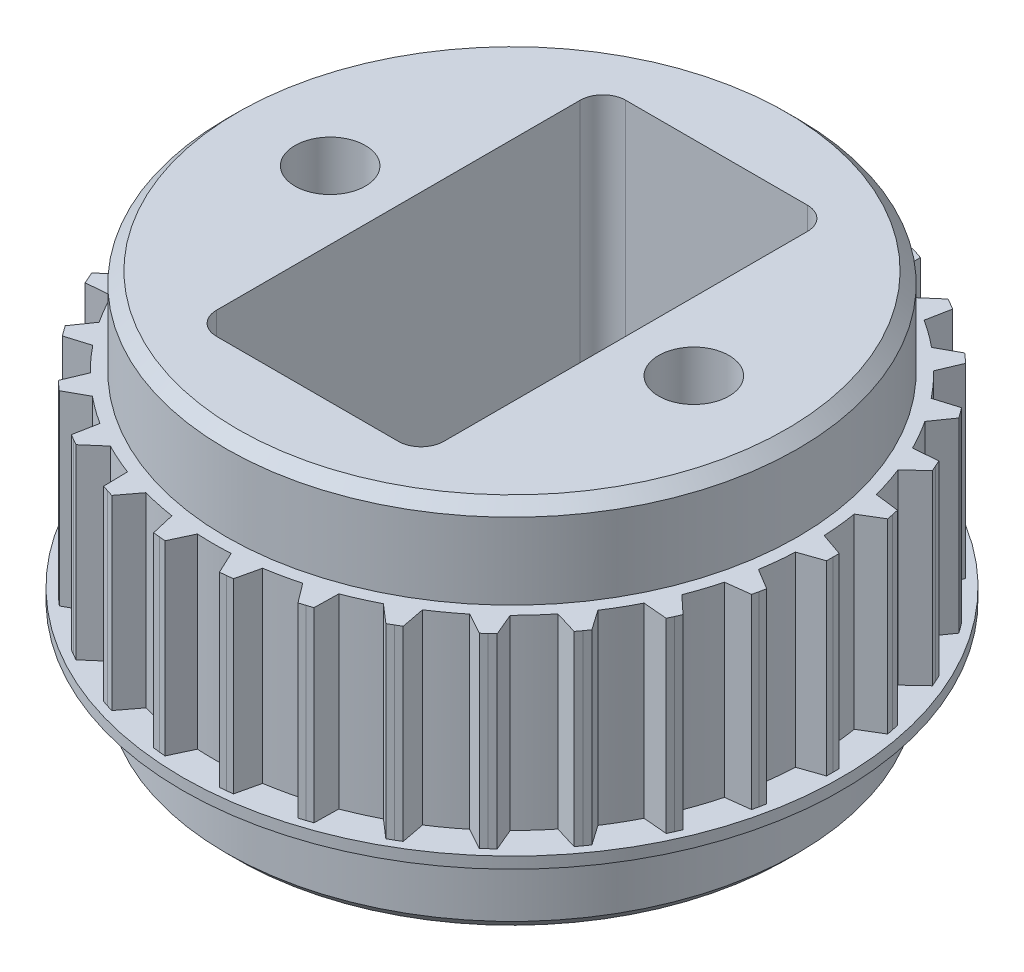
SolidWorks part; units mm, degrees
ref_plane "Front Plane" through (0, 0, 0) normal (0, 0, 1) x (1, 0, 0)
ref_plane "Top Plane" through (0, 0, 0) normal (0, 1, 0) x (1, 0, 0)
ref_plane "Right Plane" through (0, 0, 0) normal (1, 0, 0) x (0, 0, -1)
sketch "Sketch1" plane through (0, 0, 0) normal (0, 1, 0) x (1, 0, 0)
  line L0 (0, 0) -> (-13.12, 0) construction
  line L1 (-13.12, 0) -> (-15.3941, 0) construction
  line L4 (-14.12, 0) -> (-14.1172, 0.28)
  line L5 (-14.1172, 0.28) -> (-13.1049, 0.63)
  line L6 (-14.12, 0) -> (-14.1172, -0.28)
  line L7 (-14.1172, -0.28) -> (-13.1049, -0.63)
  line L8 (-13.7505, 3.209) -> (-12.6875, 3.3409)
  line L9 (-13.8669, 2.6613) -> (-12.9495, 2.1084)
  line L10 (-13.8114, 2.9357) -> (-13.8669, 2.6613)
  line L11 (-13.8114, 2.9357) -> (-13.7505, 3.209)
  line L12 (-12.7828, 5.9978) -> (-11.7156, 5.9058)
  line L13 (-13.0106, 5.4862) -> (-12.2281, 4.7547)
  line L14 (-12.8993, 5.7431) -> (-13.0106, 5.4862)
  line L15 (-12.8993, 5.7431) -> (-12.7828, 5.9978)
  line L16 (-11.2565, 8.5244) -> (-10.2318, 8.2125)
  line L17 (-11.5857, 8.0714) -> (-10.9724, 7.1932)
  line L18 (-11.4233, 8.2995) -> (-11.5857, 8.0714)
  line L19 (-11.4233, 8.2995) -> (-11.2565, 8.5244)
  line L20 (-9.2382, 10.6785) -> (-8.3007, 10.1604)
  line L21 (-9.6543, 10.3038) -> (-9.237, 9.3173)
  line L22 (-9.4481, 10.4932) -> (-9.6543, 10.3038)
  line L23 (-9.4481, 10.4932) -> (-9.2382, 10.6785)
  line L24 (-6.8161, 12.3659) -> (-6.0068, 11.6641)
  line L25 (-7.3011, 12.0859) -> (-7.098, 11.0341)
  line L26 (-7.06, 12.2283) -> (-7.3011, 12.0859)
  line L27 (-7.06, 12.2283) -> (-6.8161, 12.3659)
  line L28 (-4.0962, 13.5128) -> (-3.4505, 12.6581)
  line L29 (-4.6288, 13.3398) -> (-4.6488, 12.2688)
  line L30 (-4.3633, 13.4289) -> (-4.6288, 13.3398)
  line L31 (-4.3633, 13.4289) -> (-4.0962, 13.5128)
  line L32 (-1.1972, 14.0692) -> (-0.7433, 13.0989)
  line L33 (-1.7541, 14.0106) -> (-1.9964, 12.9672)
  line L34 (-1.4759, 14.0426) -> (-1.7541, 14.0106)
  line L35 (-1.4759, 14.0426) -> (-1.1972, 14.0692)
  line L36 (1.7541, 14.0106) -> (1.9964, 12.9672)
  line L37 (1.1972, 14.0692) -> (0.7433, 13.0989)
  line L38 (1.4759, 14.0426) -> (1.1972, 14.0692)
  line L39 (1.4759, 14.0426) -> (1.7541, 14.0106)
  line L40 (4.6287, 13.3398) -> (4.6488, 12.2688)
  line L41 (4.0962, 13.5128) -> (3.4505, 12.6581)
  line L42 (4.3633, 13.4289) -> (4.0962, 13.5128)
  line L43 (4.3633, 13.4289) -> (4.6287, 13.3398)
  line L44 (7.3011, 12.0859) -> (7.098, 11.0341)
  line L45 (6.8161, 12.3659) -> (6.0068, 11.6641)
  line L46 (7.06, 12.2283) -> (6.8161, 12.3659)
  line L47 (7.06, 12.2283) -> (7.3011, 12.0859)
  line L48 (9.6543, 10.3038) -> (9.237, 9.3173)
  line L49 (9.2382, 10.6785) -> (8.3007, 10.1604)
  line L50 (9.4481, 10.4932) -> (9.2382, 10.6785)
  line L51 (9.4481, 10.4932) -> (9.6543, 10.3038)
  line L52 (11.5856, 8.0714) -> (10.9724, 7.1932)
  line L53 (11.2565, 8.5244) -> (10.2318, 8.2125)
  line L54 (11.4233, 8.2995) -> (11.2565, 8.5244)
  line L55 (11.4233, 8.2995) -> (11.5856, 8.0714)
  line L56 (13.0106, 5.4862) -> (12.2281, 4.7547)
  line L57 (12.7828, 5.9978) -> (11.7156, 5.9058)
  line L58 (12.8993, 5.7431) -> (12.7828, 5.9978)
  line L59 (12.8993, 5.7431) -> (13.0106, 5.4862)
  line L60 (13.8669, 2.6613) -> (12.9495, 2.1084)
  line L61 (13.7505, 3.209) -> (12.6875, 3.3409)
  line L62 (13.8114, 2.9357) -> (13.7505, 3.209)
  line L63 (13.8114, 2.9357) -> (13.8669, 2.6613)
  line L64 (14.1172, -0.28) -> (13.1049, -0.63)
  line L65 (14.1172, 0.28) -> (13.1049, 0.63)
  line L66 (14.12, 0) -> (14.1172, 0.28)
  line L67 (14.12, 0) -> (14.1172, -0.28)
  line L68 (13.7505, -3.209) -> (12.6875, -3.3409)
  line L69 (13.8669, -2.6613) -> (12.9495, -2.1084)
  line L70 (13.8114, -2.9357) -> (13.8669, -2.6613)
  line L71 (13.8114, -2.9357) -> (13.7505, -3.209)
  line L72 (12.7828, -5.9978) -> (11.7156, -5.9058)
  line L73 (13.0106, -5.4862) -> (12.2281, -4.7547)
  line L74 (12.8993, -5.7431) -> (13.0106, -5.4862)
  line L75 (12.8993, -5.7431) -> (12.7828, -5.9978)
  line L76 (11.2565, -8.5244) -> (10.2318, -8.2125)
  line L77 (11.5857, -8.0714) -> (10.9724, -7.1932)
  line L78 (11.4233, -8.2995) -> (11.5857, -8.0714)
  line L79 (11.4233, -8.2995) -> (11.2565, -8.5244)
  line L80 (9.2382, -10.6785) -> (8.3007, -10.1604)
  line L81 (9.6543, -10.3038) -> (9.237, -9.3173)
  line L82 (9.4481, -10.4932) -> (9.6543, -10.3038)
  line L83 (9.4481, -10.4932) -> (9.2382, -10.6785)
  line L84 (6.8161, -12.3659) -> (6.0068, -11.6641)
  line L85 (7.3011, -12.0859) -> (7.098, -11.0341)
  line L86 (7.06, -12.2283) -> (7.3011, -12.0859)
  line L87 (7.06, -12.2283) -> (6.8161, -12.3659)
  line L88 (4.0962, -13.5128) -> (3.4505, -12.6581)
  line L89 (4.6288, -13.3398) -> (4.6488, -12.2688)
  line L90 (4.3633, -13.4289) -> (4.6288, -13.3398)
  line L91 (4.3633, -13.4289) -> (4.0962, -13.5128)
  line L92 (1.1972, -14.0692) -> (0.7433, -13.0989)
  line L93 (1.7541, -14.0106) -> (1.9964, -12.9672)
  line L94 (1.4759, -14.0426) -> (1.7541, -14.0106)
  line L95 (1.4759, -14.0426) -> (1.1972, -14.0692)
  line L96 (-1.7541, -14.0106) -> (-1.9964, -12.9672)
  line L97 (-1.1972, -14.0692) -> (-0.7433, -13.0989)
  line L98 (-1.4759, -14.0426) -> (-1.1972, -14.0692)
  line L99 (-1.4759, -14.0426) -> (-1.7541, -14.0106)
  line L100 (-4.6287, -13.3398) -> (-4.6488, -12.2688)
  line L101 (-4.0962, -13.5128) -> (-3.4505, -12.6581)
  line L102 (-4.3633, -13.4289) -> (-4.0962, -13.5128)
  line L103 (-4.3633, -13.4289) -> (-4.6287, -13.3398)
  line L104 (-7.3011, -12.0859) -> (-7.098, -11.0341)
  line L105 (-6.8161, -12.3659) -> (-6.0068, -11.6641)
  line L106 (-7.06, -12.2283) -> (-6.8161, -12.3659)
  line L107 (-7.06, -12.2283) -> (-7.3011, -12.0859)
  line L108 (-9.6543, -10.3038) -> (-9.237, -9.3173)
  line L109 (-9.2382, -10.6785) -> (-8.3007, -10.1604)
  line L110 (-9.4481, -10.4932) -> (-9.2382, -10.6785)
  line L111 (-9.4481, -10.4932) -> (-9.6543, -10.3038)
  line L112 (-11.5856, -8.0714) -> (-10.9724, -7.1932)
  line L113 (-11.2565, -8.5244) -> (-10.2318, -8.2125)
  line L114 (-11.4233, -8.2995) -> (-11.2565, -8.5244)
  line L115 (-11.4233, -8.2995) -> (-11.5856, -8.0714)
  line L116 (-13.0106, -5.4862) -> (-12.2281, -4.7547)
  line L117 (-12.7828, -5.9978) -> (-11.7156, -5.9058)
  line L118 (-12.8993, -5.7431) -> (-12.7828, -5.9978)
  line L119 (-12.8993, -5.7431) -> (-13.0106, -5.4862)
  line L120 (-13.8669, -2.6613) -> (-12.9495, -2.1084)
  line L121 (-13.7505, -3.209) -> (-12.6875, -3.3409)
  line L122 (-13.8114, -2.9357) -> (-13.7505, -3.209)
  line L123 (-13.8114, -2.9357) -> (-13.8669, -2.6613)
  circle A0 centre (0, 0) radius 13.12
  circle A2 centre (0, 0) radius 13.12
  circle A3 centre (0, 0) radius 13.12
  circle A4 centre (0, 0) radius 13.12
  circle A5 centre (0, 0) radius 13.12
  circle A6 centre (0, 0) radius 13.12
  circle A7 centre (0, 0) radius 13.12
  circle A8 centre (0, 0) radius 13.12
  circle A9 centre (0, 0) radius 13.12
  circle A10 centre (0, 0) radius 13.12
  circle A11 centre (0, 0) radius 13.12
  circle A12 centre (0, 0) radius 13.12
  circle A13 centre (0, 0) radius 13.12
  circle A14 centre (0, 0) radius 13.12
  circle A15 centre (0, 0) radius 13.12
  circle A16 centre (0, 0) radius 13.12
  circle A17 centre (0, 0) radius 13.12
  circle A18 centre (0, 0) radius 13.12
  circle A19 centre (0, 0) radius 13.12
  circle A20 centre (0, 0) radius 13.12
  circle A21 centre (0, 0) radius 13.12
  circle A22 centre (0, 0) radius 13.12
  circle A23 centre (0, 0) radius 13.12
  circle A24 centre (0, 0) radius 13.12
  circle A25 centre (0, 0) radius 13.12
  circle A26 centre (0, 0) radius 13.12
  circle A27 centre (0, 0) radius 13.12
  circle A28 centre (0, 0) radius 13.12
  circle A29 centre (0, 0) radius 13.12
  circle A30 centre (0, 0) radius 13.12
  point P187 (0, 0)
  dimension "D1" = 26.24
  dimension "D3" = 0.63
  dimension "D4" = 0.63
  dimension "D5" = 0.28
  dimension "D6" = 0.28
  dimension "D2" = 30
sketch "Sketch3" plane through (0, 0, 0) normal (0, 1, 0) x (1, 0, 0)
  circle A0 centre (0, 0) radius 13.12
extrude "Boss-Extrude1" add sketch "Sketch3" along normal blind 8.2
sketch "Sketch4" plane through (0, 0, 0) normal (0, 1, 0) x (1, 0, 0)
  line L0 (-14.1172, -0.28) -> (-13.1049, -0.63) construction
  line L1 (-14.12, 0) -> (-14.1172, -0.28) construction
  line L2 (-14.12, 0) -> (-14.1172, 0.28) construction
  line L3 (-14.1172, 0.28) -> (-13.1049, 0.63) construction
  line L4 (-14.1172, -0.28) -> (-12.8499, -0.7181)
  line L5 (-14.12, 0) -> (-14.1172, -0.28)
  line L6 (-14.12, 0) -> (-14.1172, 0.28)
  line L7 (-14.1172, 0.28) -> (-12.8499, 0.7181)
  line L8 (-13.8669, 2.6613) -> (-12.7185, 1.9692)
  line L9 (-13.8114, 2.9357) -> (-13.8669, 2.6613)
  line L10 (-13.8114, 2.9357) -> (-13.7505, 3.209)
  line L11 (-13.7505, 3.209) -> (-12.4198, 3.3741)
  line L12 (-13.0106, 5.4862) -> (-12.0311, 4.5705)
  line L13 (-12.8993, 5.7431) -> (-13.0106, 5.4862)
  line L14 (-12.8993, 5.7431) -> (-12.7828, 5.9978)
  line L15 (-12.7828, 5.9978) -> (-11.4469, 5.8826)
  line L16 (-11.5857, 8.0714) -> (-10.8179, 6.972)
  line L17 (-11.4233, 8.2995) -> (-11.5857, 8.0714)
  line L18 (-11.4233, 8.2995) -> (-11.2565, 8.5244)
  line L19 (-11.2565, 8.5244) -> (-9.9737, 8.134)
  line L20 (-9.6543, 10.3038) -> (-9.132, 9.0688)
  line L21 (-9.4481, 10.4932) -> (-9.6543, 10.3038)
  line L22 (-9.4481, 10.4932) -> (-9.2382, 10.6785)
  line L23 (-9.2382, 10.6785) -> (-8.0646, 10.0299)
  line L24 (-7.3011, 12.0859) -> (-7.0469, 10.7693)
  line L25 (-7.06, 12.2283) -> (-7.3011, 12.0859)
  line L26 (-7.06, 12.2283) -> (-6.8161, 12.3659)
  line L27 (-6.8161, 12.3659) -> (-5.8031, 11.4874)
  line L28 (-4.6288, 13.3398) -> (-4.6538, 11.9991)
  line L29 (-4.3633, 13.4289) -> (-4.6288, 13.3398)
  line L30 (-4.3633, 13.4289) -> (-4.0962, 13.5128)
  line L31 (-4.0962, 13.5128) -> (-3.2879, 12.4429)
  line L32 (-1.7541, 14.0106) -> (-2.0574, 12.7045)
  line L33 (-1.4759, 14.0426) -> (-1.7541, 14.0106)
  line L34 (-1.4759, 14.0426) -> (-1.1972, 14.0692)
  line L35 (-1.1972, 14.0692) -> (-0.629, 12.8546)
  line L36 (1.1972, 14.0692) -> (0.629, 12.8546)
  line L37 (1.4759, 14.0426) -> (1.1972, 14.0692)
  line L38 (1.4759, 14.0426) -> (1.7541, 14.0106)
  line L39 (1.7541, 14.0106) -> (2.0574, 12.7045)
  line L40 (4.0962, 13.5128) -> (3.2879, 12.4429)
  line L41 (4.3633, 13.4289) -> (4.0962, 13.5128)
  line L42 (4.3633, 13.4289) -> (4.6287, 13.3398)
  line L43 (4.6287, 13.3398) -> (4.6538, 11.9991)
  line L44 (6.8161, 12.3659) -> (5.8031, 11.4874)
  line L45 (7.06, 12.2283) -> (6.8161, 12.3659)
  line L46 (7.06, 12.2283) -> (7.3011, 12.0859)
  line L47 (7.3011, 12.0859) -> (7.0469, 10.7693)
  line L48 (9.2382, 10.6785) -> (8.0646, 10.0299)
  line L49 (9.4481, 10.4932) -> (9.2382, 10.6785)
  line L50 (9.4481, 10.4932) -> (9.6543, 10.3038)
  line L51 (9.6543, 10.3038) -> (9.132, 9.0688)
  line L52 (11.2565, 8.5244) -> (9.9737, 8.134)
  line L53 (11.4233, 8.2995) -> (11.2565, 8.5244)
  line L54 (11.4233, 8.2995) -> (11.5856, 8.0714)
  line L55 (11.5856, 8.0714) -> (10.8179, 6.972)
  line L56 (12.7828, 5.9978) -> (11.4469, 5.8826)
  line L57 (12.8993, 5.7431) -> (12.7828, 5.9978)
  line L58 (12.8993, 5.7431) -> (13.0106, 5.4862)
  line L59 (13.0106, 5.4862) -> (12.0311, 4.5705)
  line L60 (13.7505, 3.209) -> (12.4198, 3.3741)
  line L61 (13.8114, 2.9357) -> (13.7505, 3.209)
  line L62 (13.8114, 2.9357) -> (13.8669, 2.6613)
  line L63 (13.8669, 2.6613) -> (12.7185, 1.9692)
  line L64 (14.1172, 0.28) -> (12.8499, 0.7181)
  line L65 (14.12, 0) -> (14.1172, 0.28)
  line L66 (14.12, 0) -> (14.1172, -0.28)
  line L67 (14.1172, -0.28) -> (12.8499, -0.7181)
  line L68 (13.8669, -2.6613) -> (12.7185, -1.9692)
  line L69 (13.8114, -2.9357) -> (13.8669, -2.6613)
  line L70 (13.8114, -2.9357) -> (13.7505, -3.209)
  line L71 (13.7505, -3.209) -> (12.4198, -3.3741)
  line L72 (13.0106, -5.4862) -> (12.0311, -4.5705)
  line L73 (12.8993, -5.7431) -> (13.0106, -5.4862)
  line L74 (12.8993, -5.7431) -> (12.7828, -5.9978)
  line L75 (12.7828, -5.9978) -> (11.4469, -5.8826)
  line L76 (11.5857, -8.0714) -> (10.8179, -6.972)
  line L77 (11.4233, -8.2995) -> (11.5857, -8.0714)
  line L78 (11.4233, -8.2995) -> (11.2565, -8.5244)
  line L79 (11.2565, -8.5244) -> (9.9737, -8.134)
  line L80 (9.6543, -10.3038) -> (9.132, -9.0688)
  line L81 (9.4481, -10.4932) -> (9.6543, -10.3038)
  line L82 (9.4481, -10.4932) -> (9.2382, -10.6785)
  line L83 (9.2382, -10.6785) -> (8.0646, -10.0299)
  line L84 (7.3011, -12.0859) -> (7.0469, -10.7693)
  line L85 (7.06, -12.2283) -> (7.3011, -12.0859)
  line L86 (7.06, -12.2283) -> (6.8161, -12.3659)
  line L87 (6.8161, -12.3659) -> (5.8031, -11.4874)
  line L88 (4.6288, -13.3398) -> (4.6538, -11.9991)
  line L89 (4.3633, -13.4289) -> (4.6288, -13.3398)
  line L90 (4.3633, -13.4289) -> (4.0962, -13.5128)
  line L91 (4.0962, -13.5128) -> (3.2879, -12.4429)
  line L92 (1.7541, -14.0106) -> (2.0574, -12.7045)
  line L93 (1.4759, -14.0426) -> (1.7541, -14.0106)
  line L94 (1.4759, -14.0426) -> (1.1972, -14.0692)
  line L95 (1.1972, -14.0692) -> (0.629, -12.8546)
  line L96 (-1.1972, -14.0692) -> (-0.629, -12.8546)
  line L97 (-1.4759, -14.0426) -> (-1.1972, -14.0692)
  line L98 (-1.4759, -14.0426) -> (-1.7541, -14.0106)
  line L99 (-1.7541, -14.0106) -> (-2.0574, -12.7045)
  line L100 (-4.0962, -13.5128) -> (-3.2879, -12.4429)
  line L101 (-4.3633, -13.4289) -> (-4.0962, -13.5128)
  line L102 (-4.3633, -13.4289) -> (-4.6287, -13.3398)
  line L103 (-4.6287, -13.3398) -> (-4.6538, -11.9991)
  line L104 (-6.8161, -12.3659) -> (-5.8031, -11.4874)
  line L105 (-7.06, -12.2283) -> (-6.8161, -12.3659)
  line L106 (-7.06, -12.2283) -> (-7.3011, -12.0859)
  line L107 (-7.3011, -12.0859) -> (-7.0469, -10.7693)
  line L108 (-9.2382, -10.6785) -> (-8.0646, -10.0299)
  line L109 (-9.4481, -10.4932) -> (-9.2382, -10.6785)
  line L110 (-9.4481, -10.4932) -> (-9.6543, -10.3038)
  line L111 (-9.6543, -10.3038) -> (-9.132, -9.0688)
  line L112 (-11.2565, -8.5244) -> (-9.9737, -8.134)
  line L113 (-11.4233, -8.2995) -> (-11.2565, -8.5244)
  line L114 (-11.4233, -8.2995) -> (-11.5856, -8.0714)
  line L115 (-11.5856, -8.0714) -> (-10.8179, -6.972)
  line L116 (-12.7828, -5.9978) -> (-11.4469, -5.8826)
  line L117 (-12.8993, -5.7431) -> (-12.7828, -5.9978)
  line L118 (-12.8993, -5.7431) -> (-13.0106, -5.4862)
  line L119 (-13.0106, -5.4862) -> (-12.0311, -4.5705)
  line L120 (-13.7505, -3.209) -> (-12.4198, -3.3741)
  line L121 (-13.8114, -2.9357) -> (-13.7505, -3.209)
  line L122 (-13.8114, -2.9357) -> (-13.8669, -2.6613)
  line L123 (-13.8669, -2.6613) -> (-12.7185, -1.9692)
  arc A1 (-12.4198, 3.3741) -> (-12.7185, 1.9692) centre (0, 0) ccw
  circle A2 centre (0, 0) radius 12.87
  arc A3 (-12.8499, 0.7181) -> (-12.8499, -0.7181) centre (0, 0) ccw
  arc A4 (-11.4469, 5.8826) -> (-12.0311, 4.5705) centre (0, 0) ccw
  arc A5 (-9.9737, 8.134) -> (-10.8179, 6.972) centre (0, 0) ccw
  arc A6 (-8.0646, 10.0299) -> (-9.132, 9.0688) centre (0, 0) ccw
  arc A7 (-5.8031, 11.4874) -> (-7.0469, 10.7693) centre (0, 0) ccw
  arc A8 (-3.2879, 12.4429) -> (-4.6538, 11.9991) centre (0, 0) ccw
  arc A9 (-0.629, 12.8546) -> (-2.0574, 12.7045) centre (0, 0) ccw
  arc A10 (2.0574, 12.7045) -> (0.629, 12.8546) centre (0, 0) ccw
  arc A11 (4.6538, 11.9991) -> (3.2879, 12.4429) centre (0, 0) ccw
  arc A12 (7.0469, 10.7693) -> (5.8031, 11.4874) centre (0, 0) ccw
  arc A13 (9.132, 9.0688) -> (8.0646, 10.0299) centre (0, 0) ccw
  arc A14 (10.8179, 6.972) -> (9.9737, 8.134) centre (0, 0) ccw
  arc A15 (12.0311, 4.5705) -> (11.4469, 5.8826) centre (0, 0) ccw
  arc A16 (12.7185, 1.9692) -> (12.4198, 3.3741) centre (0, 0) ccw
  arc A17 (12.8499, -0.7181) -> (12.8499, 0.7181) centre (0, 0) ccw
  arc A18 (12.4198, -3.3741) -> (12.7185, -1.9692) centre (0, 0) ccw
  arc A19 (11.4469, -5.8826) -> (12.0311, -4.5705) centre (0, 0) ccw
  arc A20 (9.9737, -8.134) -> (10.8179, -6.972) centre (0, 0) ccw
  arc A21 (8.0646, -10.0299) -> (9.132, -9.0688) centre (0, 0) ccw
  arc A22 (5.8031, -11.4874) -> (7.0469, -10.7693) centre (0, 0) ccw
  arc A23 (3.2879, -12.4429) -> (4.6538, -11.9991) centre (0, 0) ccw
  arc A24 (0.629, -12.8546) -> (2.0574, -12.7045) centre (0, 0) ccw
  arc A25 (-2.0574, -12.7045) -> (-0.629, -12.8546) centre (0, 0) ccw
  arc A26 (-4.6538, -11.9991) -> (-3.2879, -12.4429) centre (0, 0) ccw
  arc A27 (-7.0469, -10.7693) -> (-5.8031, -11.4874) centre (0, 0) ccw
  arc A28 (-9.132, -9.0688) -> (-8.0646, -10.0299) centre (0, 0) ccw
  arc A29 (-10.8179, -6.972) -> (-9.9737, -8.134) centre (0, 0) ccw
  arc A30 (-12.0311, -4.5705) -> (-11.4469, -5.8826) centre (0, 0) ccw
  arc A31 (-12.7185, -1.9692) -> (-12.4198, -3.3741) centre (0, 0) ccw
  point P156 (0, 0)
  dimension "D1" = 0.25
  dimension "D2" = 30
extrude "Boss-Extrude2" add sketch "Sketch4" along normal up to surface (8.2 mm away) up to face at (0, 8.2, 13.12)
sketch "Sketch5" plane through (0, 0, 0) normal (0, -1, 0) x (1, 0, 0)
  circle A0 centre (0, 0) radius 14.5
  dimension "D1" = 29
extrude "Boss-Extrude3" add sketch "Sketch5" along normal blind 0.5
sketch "Sketch6" plane through (0, -0.5, 0) normal (0, -1, 0) x (-1, 0, 0)
  circle A0 centre (0, 0) radius 12.575
  dimension "D1" = 25.15
extrude "Boss-Extrude4" add sketch "Sketch6" along normal blind 3.85
sketch "Sketch7" plane through (0, 8.2, 0) normal (0, 1, 0) x (1, 0, 0)
  circle A0 centre (0, 0) radius 12.575
  dimension "D1" = 25.15
extrude "Boss-Extrude5" add sketch "Sketch7" along normal blind 3.85
chamfer "Chamfer1" distance 0.5 angle 45 2 edges at (0, -4.35, -12.575) (0, 12.05, 12.575)
sketch "Sketch8" plane through (0, 12.05, 0) normal (0, 1, 0) x (1, 0, 0)
  line L1 (5, -9) -> (-5, -9)
  line L2 (5, -9) -> (5, 9)
  line L3 (5, 9) -> (-5, 9)
  line L4 (-5, -9) -> (-5, 9)
  line L5 (5, -9) -> (-5, 9) construction
  line L6 (5, 9) -> (-5, -9) construction
  point P0 (0, 0)
  dimension "D1" = 10
  dimension "D2" = 18
extrude "Cut-Extrude1" cut sketch "Sketch8" against normal through all both and the other way through all
sketch "Sketch9" plane through (0, 12.05, 0) normal (0, 1, 0) x (1, 0, 0)
  line L0 (0, 0) -> (-8, 0) construction
  line L1 (0, 0) -> (8, 0) construction
  circle A0 centre (-8, 0) radius 1.55
  circle A1 centre (8, 0) radius 1.55
  dimension "D3" = 3.1
  dimension "D4" = 3.1
  dimension "D1" = 8
  dimension "D2" = 8
extrude "Cut-Extrude2" cut sketch "Sketch9" against normal through all both
fillet "Fillet1" radius 1 4 edges at (-5, 3.85, 9) (5, 3.85, 9) (5, 3.85, -9) (-5, 3.85, -9)
